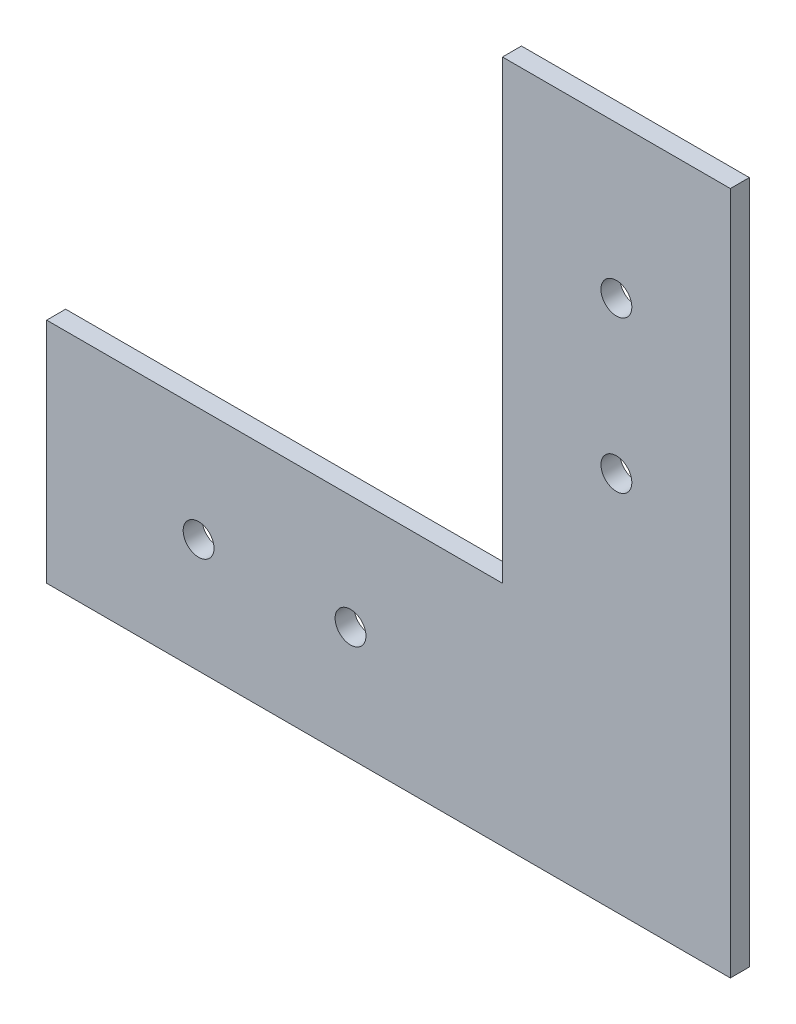
SolidWorks part; units mm, degrees
ref_plane "Front Plane" through (0, 0, 0) normal (0, 0, 1) x (1, 0, 0)
ref_plane "Top Plane" through (0, 0, 0) normal (0, 1, 0) x (1, 0, 0)
ref_plane "Right Plane" through (0, 0, 0) normal (1, 0, 0) x (0, 0, -1)
sketch "Sketch1" plane through (0, 0, 0) normal (0, 0, 1) x (1, 0, 0)
  line L0 (44.2368, 51.4865) -> (82.3368, 51.4865)
  line L1 (82.3368, 51.4865) -> (82.3368, -62.8135)
  line L2 (82.3368, -62.8135) -> (-31.9632, -62.8135)
  line L3 (-31.9632, -62.8135) -> (-31.9632, -24.7135)
  line L4 (-31.9632, -24.7135) -> (44.2368, -24.7135)
  line L5 (44.2368, -24.7135) -> (44.2368, 51.4865)
  dimension "D1" = 38.1
  dimension "D2" = 38.1
  dimension "D3" = 114.3
  dimension "D4" = 114.3
extrude "Boss-Extrude1" add sketch "Sketch1" along normal blind 3.175
sketch "Sketch2" plane through (0, 0, 3.175) normal (0, 0, 1) x (1, 0, 0)
  line L0 (44.2368, -24.7135) -> (-31.9632, -24.7135) construction
  line L1 (82.3368, -62.8135) -> (82.3368, 51.4865) construction
  line L2 (82.3368, 51.4865) -> (44.2368, 51.4865) construction
  line L3 (-31.9632, -24.7135) -> (-31.9632, -62.8135) construction
  circle A0 centre (63.2868, 26.0865) radius 2.5797
  circle A1 centre (63.2868, 0.6865) radius 2.5797
  circle A2 centre (-6.5632, -43.7635) radius 2.5797
  circle A3 centre (18.8368, -43.7635) radius 2.5797
  dimension "D1" = 5.1594
  dimension "D2" = 5.1594
  dimension "D3" = 5.1594
  dimension "D4" = 5.1594
  dimension "D5" = 19.05
  dimension "D6" = 19.05
  dimension "D7" = 19.05
  dimension "D8" = 19.05
  dimension "D9" = 25.4
  dimension "D10" = 50.8
  dimension "D11" = 50.8
  dimension "D12" = 25.4
extrude "Cut-Extrude1" cut sketch "Sketch2" against normal blind 3.175
